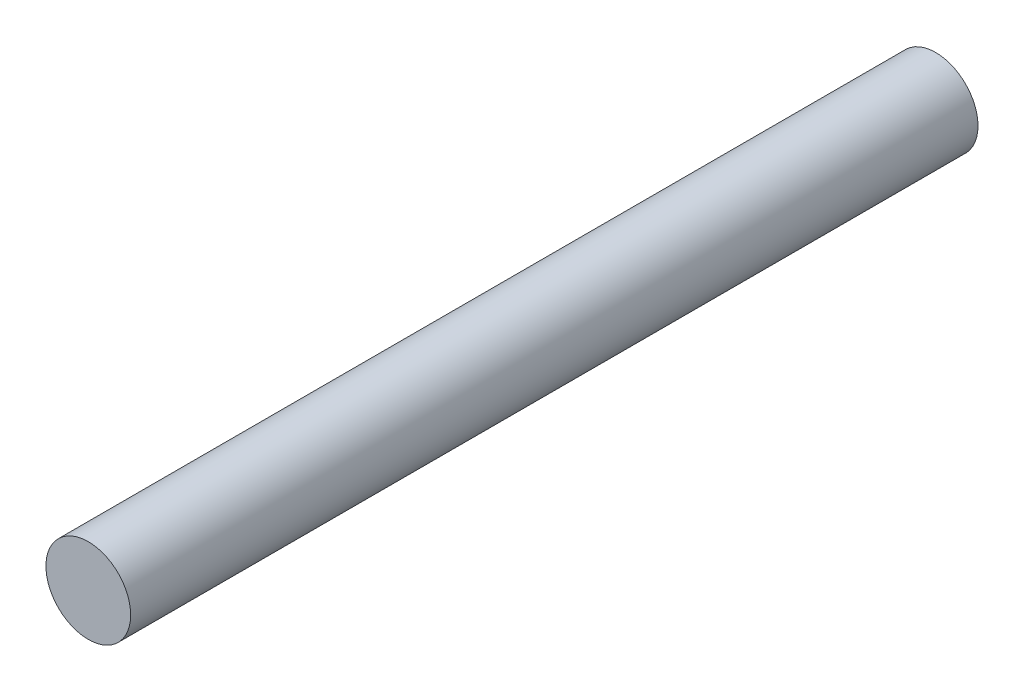
SolidWorks part; units mm, degrees
ref_plane "Plan de face" through (0, 0, 0) normal (0, 0, 1) x (1, 0, 0)
ref_plane "Plan de dessus" through (0, 0, 0) normal (0, 1, 0) x (1, 0, 0)
ref_plane "Plan de droite" through (0, 0, 0) normal (1, 0, 0) x (0, 0, -1)
sketch "Esquisse1" plane through (0, 0, 0) normal (0, 0, 1) x (1, 0, 0)
  circle A0 centre (0, 0) radius 4
  dimension "D1" = 8
extrude "Boss.-Extru.1" add sketch "Esquisse1" along normal blind 80
